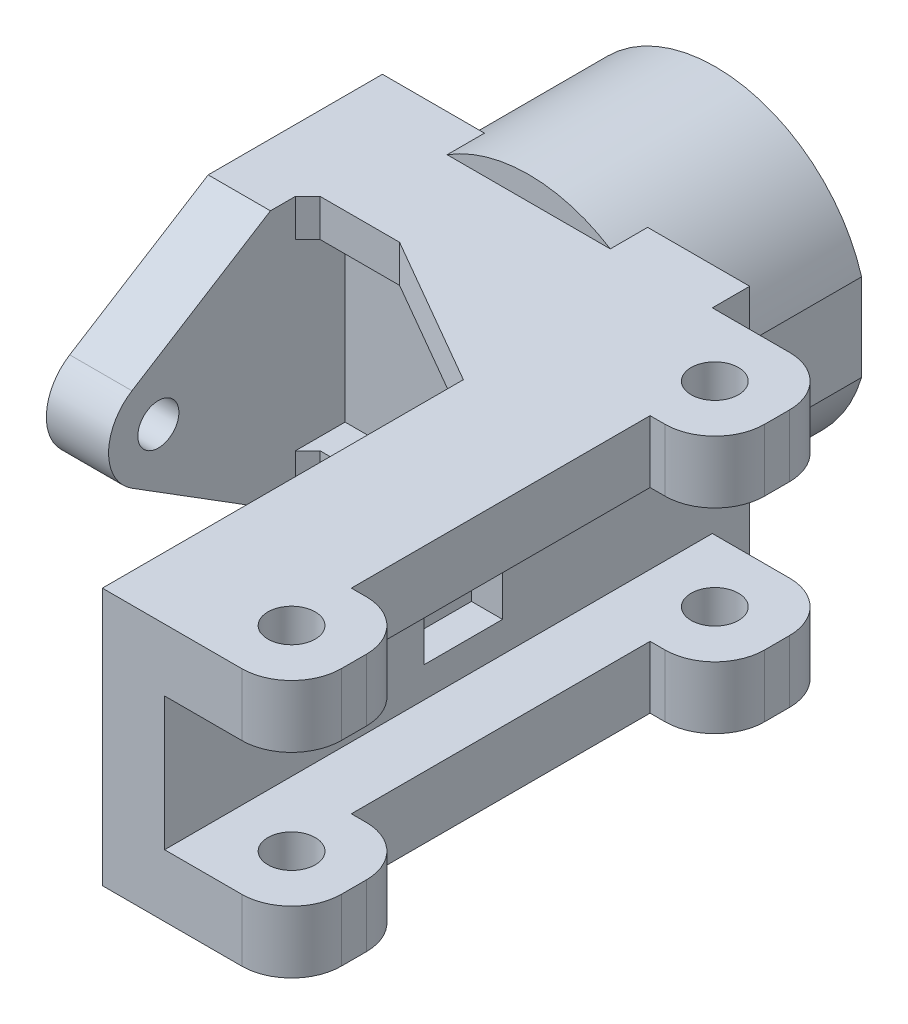
SolidWorks part; units mm, degrees
ref_plane "正面(Front)" through (0, 0, 0) normal (0, 0, 1) x (1, 0, 0)
ref_plane "平面(Top)" through (0, 0, 0) normal (0, 1, 0) x (1, 0, 0)
ref_plane "右側面(Right)" through (0, 0, 0) normal (1, 0, 0) x (0, 0, -1)
sketch "ｽｹｯﾁ1" plane through (0, 0, 0) normal (0, 0, 1) x (1, 0, 0)
  circle A0 centre (0, 0) radius 6.325
  dimension "D1" = 12.65
extrude "ﾎﾞｽ - 押し出し1" add sketch "ｽｹｯﾁ1" against normal blind 15
sketch "ｽｹｯﾁ2" plane through (0, 0, 0) normal (0, 0, 1) x (1, 0, 0)
  line L1 (-14.75, 10.35) -> (14.75, 10.35)
  line L2 (-14.75, 10.35) -> (-14.75, -10.35)
  line L3 (-14.75, -10.35) -> (14.75, -10.35)
  line L4 (14.75, 10.35) -> (14.75, -10.35)
  line L5 (-14.75, 10.35) -> (14.75, -10.35) construction
  line L6 (-14.75, -10.35) -> (14.75, 10.35) construction
  point P0 (0, 0)
  dimension "D1" = 20.7
  dimension "D2" = 29.5
extrude "ﾎﾞｽ - 押し出し2" add sketch "ｽｹｯﾁ2" along normal blind 5
sketch "ｽｹｯﾁ3" plane through (14.75, 0, 0) normal (1, 0, 0) x (0, 0, -1)
  line L0 (0, 0) -> (-31.0876, 0) construction
  line L1 (-5, 10.35) -> (-44, 10.35)
  line L3 (-44, 10.35) -> (-44, -10.35)
  line L6 (-5, -10.35) -> (-44, -10.35)
  line L7 (-5, 10.35) -> (-5, -10.35)
  circle A0 centre (-20, 0) radius 1.65
  dimension "D2" = 15
  dimension "D4" = 3.3
  dimension "D1" = 39
extrude "ﾎﾞｽ - 押し出し3" add sketch "ｽｹｯﾁ3" against normal blind 5
sketch "ｽｹｯﾁ4" plane through (14.75, 0, 0) normal (1, 0, 0) x (0, 0, -1)
  line L1 (0, 10.35) -> (-10, 10.35)
  line L2 (0, 10.35) -> (0, 5.35)
  line L3 (0, 5.35) -> (-10, 5.35)
  line L4 (-10, 10.35) -> (-10, 5.35)
  line L5 (0, -10.35) -> (-10, -10.35)
  line L6 (0, -10.35) -> (0, -5.35)
  line L7 (0, -5.35) -> (-10, -5.35)
  line L8 (-10, -10.35) -> (-10, -5.35)
  line L9 (-44, 10.35) -> (-34, 10.35)
  line L10 (-44, 10.35) -> (-44, 5.35)
  line L11 (-44, 5.35) -> (-34, 5.35)
  line L12 (-34, 10.35) -> (-34, 5.35)
  line L13 (-44, -10.35) -> (-34, -10.35)
  line L14 (-44, -10.35) -> (-44, -5.35)
  line L15 (-44, -5.35) -> (-34, -5.35)
  line L16 (-34, -10.35) -> (-34, -5.35)
  dimension "D1" = 5
  dimension "D2" = 5
  dimension "D3" = 10
  dimension "D4" = 10
extrude "ﾎﾞｽ - 押し出し4" add sketch "ｽｹｯﾁ4" along normal blind 10.2
sketch "ｽｹｯﾁ5" plane through (0, -10.35, 0) normal (0, -1, 0) x (1, 0, 0)
  line L4 (24.95, 5) -> (5.2641, 5) construction
  line L5 (24.95, 10) -> (24.95, 0) construction
  line L6 (24.95, 39) -> (4.1235, 39) construction
  line L7 (24.95, 44) -> (24.95, 34) construction
  circle A0 centre (19.95, 5) radius 1.9
  circle A2 centre (19.95, 39) radius 1.9
  dimension "D1" = 3.8
  dimension "D2" = 5
extrude "ｶｯﾄ - 押し出し1" cut sketch "ｽｹｯﾁ5" against normal through all
fillet "ﾌｨﾚｯﾄ1" radius 4 8 edges at (24.95, 7.85, 10) (24.95, 7.85, 0) (24.95, -7.85, 0) (24.95, -7.85, 10) (24.95, -7.85, 34) (24.95, 7.85, 34) (24.95, 7.85, 44) (24.95, -7.85, 44)
sketch "ｽｹｯﾁ8" plane through (14.75, 0, 0) normal (1, 0, 0) x (0, 0, -1)
  line L1 (-34, 10.35) -> (-10, 10.35)
  line L2 (-34, 10.35) -> (-34, 5.35)
  line L3 (-34, 5.35) -> (-10, 5.35)
  line L4 (-10, 10.35) -> (-10, 5.35)
  line L5 (-34, -5.35) -> (-10, -5.35)
  line L6 (-34, -5.35) -> (-34, -10.35)
  line L7 (-34, -10.35) -> (-10, -10.35)
  line L8 (-10, -5.35) -> (-10, -10.35)
extrude "ﾎﾞｽ - 押し出し6" add sketch "ｽｹｯﾁ8" along normal blind 5
sketch "ｽｹｯﾁ9" plane through (-14.75, 0, 0) normal (-1, 0, 0) x (0, 0, 1)
  line L0 (0, 0) -> (29.5336, 0) construction
  line L1 (5, 10.35) -> (11, 10.35)
  line L2 (5, 10.35) -> (44, 10.35) construction
  line L3 (11, 10.35) -> (22.1218, 3.3909)
  line L4 (11, -10.35) -> (22.1218, -3.3909)
  line L5 (5, -10.35) -> (11, -10.35)
  line L6 (5, -10.35) -> (5, 10.35)
  arc A0 (22.1218, 3.3909) -> (22.1218, -3.3909) centre (20, 0) cw
  circle A2 centre (20, 0) radius 1.65 construction
  circle A3 centre (20, 0) radius 1.65
  dimension "D1" = 4
  dimension "D3" = 3.3
  dimension "D2" = 6
extrude "ﾎﾞｽ - 押し出し7" add sketch "ｽｹｯﾁ9" against normal blind 5
sketch "ｽｹｯﾁ6" plane through (0, -10.35, 0) normal (0, -1, 0) x (1, 0, 0)
  line L3 (-9.75, 5) -> (9.75, 5) construction
  line L8 (9.75, 44) -> (9.75, 5) construction
  line L9 (-9.75, 5) -> (9.75, 5)
  line L10 (9.75, 5) -> (9.75, 15)
  line L11 (-9.75, 5) -> (9.75, 5) construction
  line L12 (-9.75, 5) -> (-9.75, 8)
  line L13 (-9.75, 5) -> (-9.75, 11) construction
  line L15 (-9.75, 8) -> (-2.3744, 8)
  line L16 (-2.3744, 8) -> (9.75, 15)
  dimension "D1" = 30
  dimension "D2" = 10
extrude "ﾎﾞｽ - 押し出し5" add sketch "ｽｹｯﾁ6" against normal blind 3
mirror "ﾐﾗｰ1" about plane through (0, 0, 0) normal (0, 1, 0) of "ﾎﾞｽ - 押し出し5"
chamfer "面取り1" [suppressed] distance 1 angle 45
chamfer "面取り2" distance 1 angle 45 2 edges at (-9.75, 8.85, 8) (-9.75, -8.85, 8)
sketch "ｽｹｯﾁ10" plane through (14.75, 0, 0) normal (1, 0, 0) x (0, 0, -1)
  line L1 (-23.15, 2.9) -> (-16.85, 2.9)
  line L2 (-23.15, 2.9) -> (-23.15, -2.9)
  line L3 (-23.15, -2.9) -> (-16.85, -2.9)
  line L4 (-16.85, 2.9) -> (-16.85, -2.9)
  line L5 (-23.15, 2.9) -> (-16.85, -2.9) construction
  line L6 (-23.15, -2.9) -> (-16.85, 2.9) construction
  point P0 (-20, 0)
  dimension "D1" = 5.8
  dimension "D2" = 6.3
extrude "ｶｯﾄ - 押し出し2" cut sketch "ｽｹｯﾁ10" against normal blind 2.5
sketch "ｽｹｯﾁ11" plane through (0, 0, 0) normal (1, 0, 0) x (0, 0, -1)
  line L0 (0, 0) -> (15, 0) construction
  line L1 (15, -6.325) -> (15, 6.325) construction
  line L2 (0, -6.325) -> (0, 6.325) construction
  circle A0 centre (7.5, 0) radius 1.65
  dimension "D1" = 3.3
  dimension "D2" = 7.5
extrude "ｶｯﾄ - 押し出し3" cut sketch "ｽｹｯﾁ11" against normal through all both and the other way through all
chamfer "面取り3" distance 1 angle 45 1 edges at (6.325, 0, -15)
sketch "ｽｹｯﾁ12" plane through (0, 10.35, 0) normal (0, 1, 0) x (1, 0, 0)
  line L0 (-20.8566, 0) -> (30.6219, 0)
extrude "ｶｯﾄ - 押し出し4" cut sketch "ｽｹｯﾁ12" against normal through all and the other way through all
sketch "ｽｹｯﾁ13" plane through (0, 0, 0) normal (0, 0, -1) x (-1, 0, 0)
  circle A0 centre (0, 0) radius 9.25
  circle A1 centre (0, 0) radius 12.25
  dimension "D1" = 18.5
  dimension "D2" = 3
extrude "ﾎﾞｽ - 押し出し8" add sketch "ｽｹｯﾁ13" along normal blind 15
sketch "ｽｹｯﾁ14" plane through (0, 0, 0) normal (1, 0, 0) x (0, 0, -1)
  line L0 (0, 0) -> (21.1695, 0) construction
  line L1 (0, -5.35) -> (0, 5.35) construction
  circle A0 centre (7.5, 0) radius 1.65
  dimension "D1" = 3.3
  dimension "D2" = 7.5
extrude "ｶｯﾄ - 押し出し5" cut sketch "ｽｹｯﾁ14" against normal through all both and the other way through all
sketch "ｽｹｯﾁ15" plane through (0, 0, -15) normal (0, 0, -1) x (-1, 0, 0)
  line L0 (-11.7394, 3.5) -> (-11.7394, -3.5)
  line L1 (-11.7394, -3.5) -> (-15.8764, -3.5)
  line L2 (-15.8764, -3.5) -> (-15.8764, 3.5)
  line L3 (-15.8764, 3.5) -> (-11.7394, 3.5)
  line L4 (0, 0) -> (0, 13.6834) construction
  line L5 (15.8764, -3.5) -> (15.8764, 3.5)
  line L6 (11.7394, -3.5) -> (15.8764, -3.5)
  line L7 (11.7394, 3.5) -> (11.7394, -3.5)
  line L8 (15.8764, 3.5) -> (11.7394, 3.5)
  circle A0 centre (0, 0) radius 12.25 construction
  arc A1 (-6.5529, 10.35) -> (-6.5529, -10.35) centre (0, 0) ccw construction
  dimension "D1" = 7
extrude "ｶｯﾄ - 押し出し6" cut sketch "ｽｹｯﾁ15" against normal up to surface (15 mm away) up to face at (16.5129, 0, 0)
sketch "ｽｹｯﾁ16" plane through (0, 0, 0) normal (0, 0, -1) x (-1, 0, 0)
  line L0 (0, 0) -> (0, 15.5048) construction
  line L1 (-11.7394, 3.5) -> (-11.7394, -3.5)
  line L2 (-14.75, 10.35) -> (-6.5529, 10.35)
  line L3 (-14.75, -10.35) -> (-14.75, 10.35)
  line L4 (6.5529, -10.35) -> (14.75, -10.35)
  line L6 (6.5529, -10.35) -> (14.75, -10.35)
  line L7 (11.7394, 3.5) -> (11.7394, -3.5)
  line L11 (11.7394, 3.5) -> (11.7394, -3.5)
  line L12 (-6.5529, -10.35) -> (-14.75, -10.35)
  line L13 (-6.5529, -10.35) -> (-20.95, -10.35) construction
  line L14 (-20.95, 10.35) -> (-6.5529, 10.35) construction
  line L18 (14.75, -10.35) -> (14.75, 10.35)
  line L20 (14.75, -10.35) -> (14.75, 10.35)
  line L21 (14.75, 10.35) -> (6.5529, 10.35)
  line L22 (14.75, 10.35) -> (6.5529, 10.35)
  arc A0 (-6.5529, -10.35) -> (-11.7394, -3.5) centre (0, 0) cw
  arc A1 (-11.7394, 3.5) -> (-6.5529, 10.35) centre (0, 0) cw
  arc A2 (11.7394, 3.5) -> (6.5529, 10.35) centre (0, 0) ccw
  arc A3 (6.5529, -10.35) -> (11.7394, -3.5) centre (0, 0) ccw
  arc A4 (11.7394, 3.5) -> (6.5529, 10.35) centre (0, 0) ccw
  arc A5 (6.5529, -10.35) -> (11.7394, -3.5) centre (0, 0) ccw
  dimension "D1" = 0
extrude "ﾎﾞｽ - 押し出し9" add sketch "ｽｹｯﾁ16" along normal blind 3
